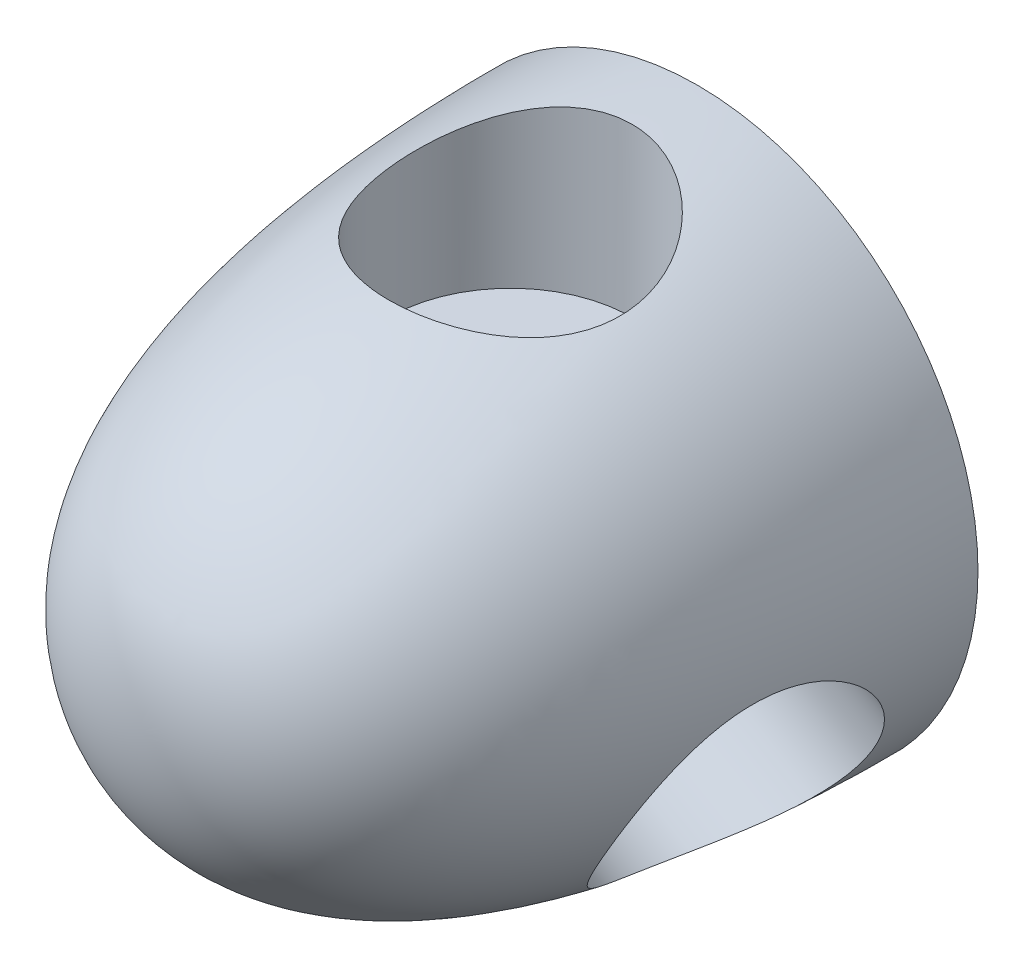
SolidWorks part; units mm, degrees
ref_plane "Front Plane" through (0, 0, 0) normal (0, 0, 1) x (1, 0, 0)
ref_plane "Top Plane" through (0, 0, 0) normal (0, 1, 0) x (1, 0, 0)
ref_plane "Right Plane" through (0, 0, 0) normal (1, 0, 0) x (0, 0, -1)
sketch "Sketch1" plane through (0, 0, 0) normal (1, 0, 0) x (0, 0, -1)
  line L0 (0, 0) -> (38.1, 0)
  line L1 (38.1, 0) -> (38.1, 19.05)
  line L3 (38.1, 19.05) -> (0, 19.05) construction
  line L4 (0, 19.05) -> (0, 0) construction
  spline S0 degree 3 poles (0, 0) (0, 16.9337) (23.901, 19.05) (38.1, 19.05) knots 0 0 0 0 1 1 1 1
  dimension "D1" = 38.1
  dimension "D2" = 19.05
revolve "Revolve1" add sketch "Sketch1" angle 360 about L0
sketch "Sketch2" plane through (0, 0, -38.1) normal (0, 0, -1) x (-1, 0, 0)
  circle A0 centre (0, 0) radius 4.826
  dimension "D1" = 9.652
extrude "Cut-Extrude1" cut sketch "Sketch2" against normal blind 12.7
ref_plane "Plane2" through (0, 7.62, 0) normal (0, 1, 0) x (1, 0, 0)
sketch "Sketch4" plane through (0, 7.62, 0) normal (0, 1, 0) x (1, 0, 0)
  line L0 (19.05, 38.1) -> (-19.05, 38.1) construction
  line L1 (19.05, 38.1) -> (-19.05, 38.1)
  line L2 (0, 38.1) -> (0, 25.4) construction
  circle A0 centre (0, 25.4) radius 8.255
  dimension "D1" = 16.51
extrude "Cut-Extrude3" cut sketch "Sketch4" along normal blind 16.256 contours A0
pattern_circular "CirPattern1" count 3 over 360 about axis through (0, 0, 0) along (0, 0, 1) of "Cut-Extrude3"
